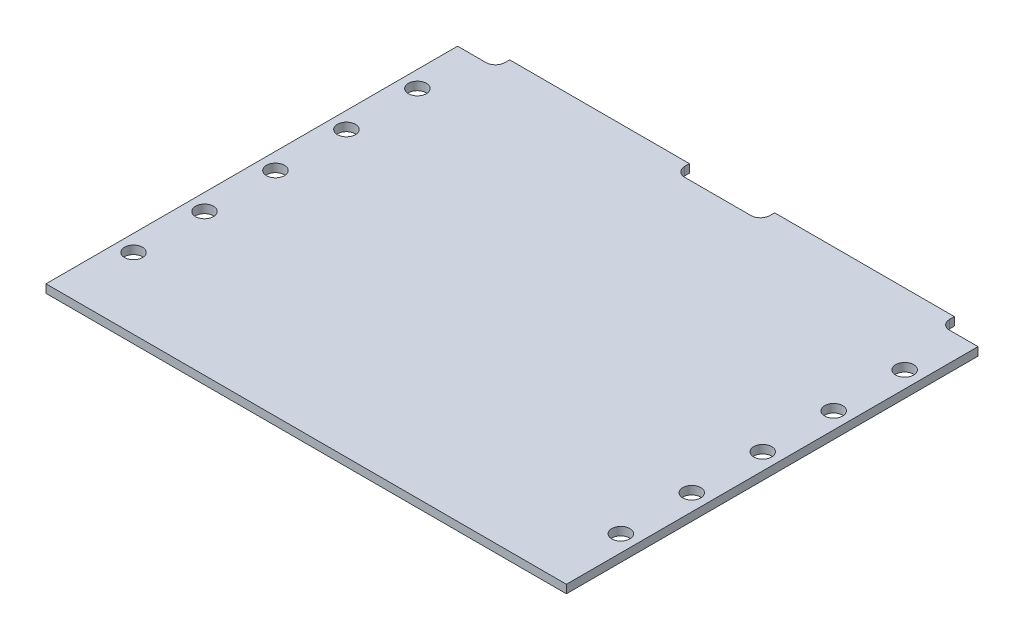
SolidWorks part; units mm, degrees
ref_plane "Front Plane" through (0, 0, 0) normal (0, 0, 1) x (1, 0, 0)
ref_plane "Top Plane" through (0, 0, 0) normal (0, 1, 0) x (1, 0, 0)
ref_plane "Right Plane" through (0, 0, 0) normal (1, 0, 0) x (0, 0, -1)
sketch "Sketch1" plane through (0, 0, 0) normal (0, 1, 0) x (1, 0, 0)
  line L0 (0, 0) -> (110, 0)
  line L1 (110, 0) -> (110, 87)
  line L2 (0, 0) -> (110, 0) construction
  line L3 (0, 0) -> (0, 87)
  line L4 (0, 87) -> (110, 87) construction
  line L5 (0, 90) -> (110, 90) construction
  line L6 (102, 90) -> (102, 89)
  line L7 (0, 0) -> (110, 0) construction
  line L8 (110, 90) -> (110, 0) construction
  line L9 (104, 87) -> (110, 87)
  line L10 (102, 90) -> (64, 90)
  line L11 (48, 87) -> (62, 87)
  line L12 (110, 0) -> (110, 90) construction
  line L13 (110, 90) -> (0, 90) construction
  line L14 (0, 90) -> (0, 0) construction
  line L15 (8, 90) -> (46, 90)
  line L16 (64, 90) -> (64, 89)
  line L18 (0, 87) -> (6, 87)
  line L20 (8, 90) -> (8, 89)
  line L21 (46, 90) -> (46, 89)
  arc A2 (46, 89) -> (48, 87) centre (48, 89) ccw
  arc A3 (102, 89) -> (104, 87) centre (104, 89) ccw
  arc A4 (64, 89) -> (62, 87) centre (62, 89) cw
  arc A8 (8, 89) -> (6, 87) centre (6, 89) cw
extrude "FR4" add sketch "Sketch1" along normal blind 1.7526
ref_plane "center-of-slot" through (0, 0.8763, 0) normal (0, -1, 0) x (-1, 0, 0)
sketch "Sketch7" plane through (0, 1.7526, 0) normal (0, 1, 0) x (1, 0, 0)
  circle A0 centre (3.5, 15) radius 1.905
  circle A1 centre (106.5, 15) radius 1.905
  circle A2 centre (106.5, 30) radius 1.905
  circle A3 centre (106.5, 45) radius 1.905
  circle A4 centre (106.5, 60) radius 1.905
  circle A5 centre (106.5, 75) radius 1.905
  circle A6 centre (3.5, 30) radius 1.905
  circle A7 centre (3.5, 45) radius 1.905
  circle A8 centre (3.5, 60) radius 1.905
  circle A9 centre (3.5, 75) radius 1.905
  dimension "D1" = 2
  dimension "D2" = 5
extrude "Cut-Extrude1" cut sketch "Sketch7" against normal through all
